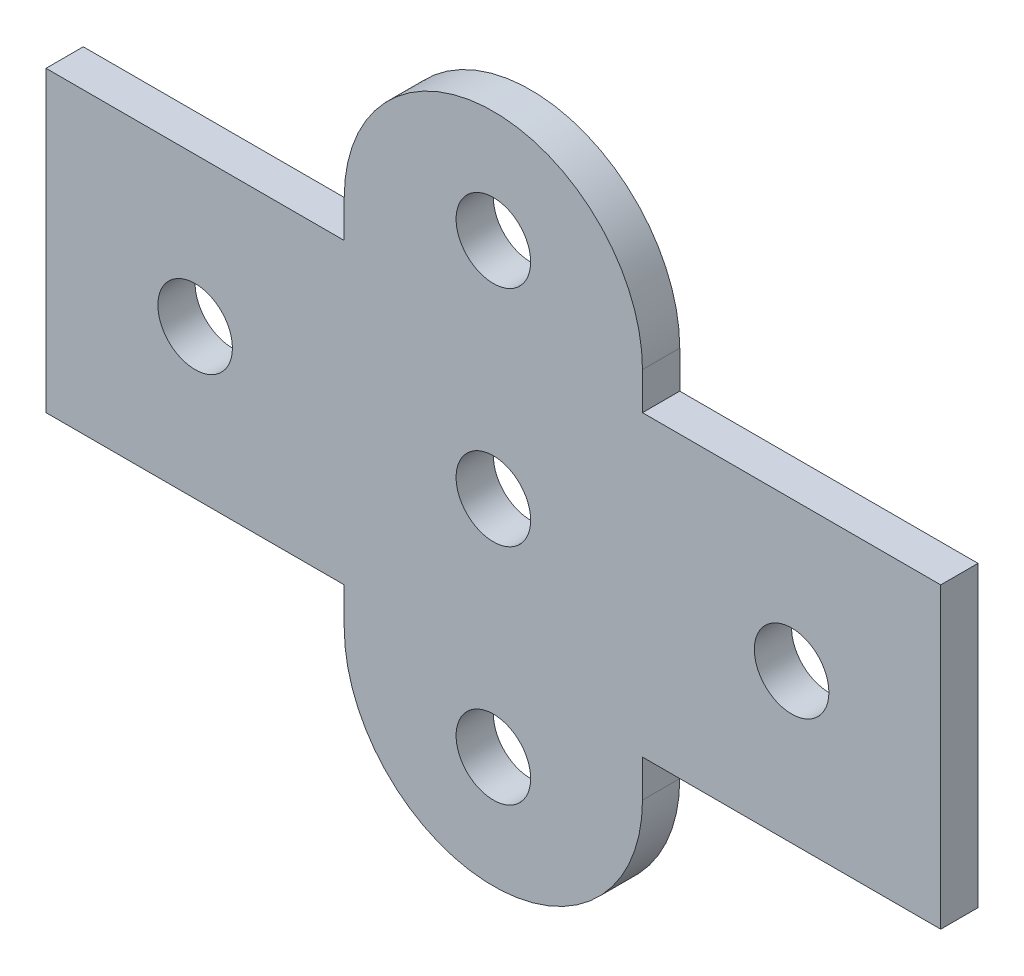
SolidWorks part; units mm, degrees
ref_plane "Front Plane" through (0, 0, 0) normal (0, 0, 1) x (1, 0, 0)
ref_plane "Top Plane" through (0, 0, 0) normal (0, 1, 0) x (1, 0, 0)
ref_plane "Right Plane" through (0, 0, 0) normal (1, 0, 0) x (0, 0, -1)
sketch "Sketch1" plane through (0, 0, 0) normal (0, 0, 1) x (1, 0, 0)
  line L0 (0, 12.7) -> (25.4, 12.7) construction
  line L1 (0, 0) -> (25.4, 0) construction
  line L2 (0, 0) -> (0, 50.8) construction
  line L3 (0, 50.8) -> (25.4, 50.8) construction
  line L4 (25.4, 0) -> (25.4, 50.8) construction
  line L5 (12.7, 50.8) -> (12.7, 0) construction
  line L6 (0, 25.4) -> (25.4, 25.4) construction
  line L7 (25.4, 38.1) -> (0, 38.1) construction
  line L8 (0, 38.1) -> (-25.4, 38.1)
  line L9 (-25.4, 38.1) -> (-25.4, 12.7)
  line L10 (-25.4, 12.7) -> (0, 12.7)
  line L11 (25.4, 38.1) -> (50.8, 38.1)
  line L12 (50.8, 38.1) -> (50.8, 12.7)
  line L13 (50.8, 12.7) -> (25.4, 12.7)
  line L14 (25.4, 38.1) -> (25.4, 41.275)
  line L15 (0, 38.1) -> (0, 41.275)
  line L16 (25.4, 12.7) -> (25.4, 9.525)
  line L17 (0, 12.7) -> (0, 9.525)
  circle A0 centre (12.7, 44.45) radius 3.175
  circle A1 centre (12.7, 6.35) radius 3.175
  circle A2 centre (12.7, 44.45) radius 6.35 construction
  arc A3 (0, 41.275) -> (25.4, 41.275) centre (12.7, 41.275) cw
  arc A4 (0, 9.525) -> (25.4, 9.525) centre (12.7, 9.525) ccw
  circle A5 centre (12.7, 25.4) radius 3.175
  circle A6 centre (38.1, 25.4) radius 3.175
  circle A7 centre (-12.7, 25.4) radius 3.175
  point P34 (0, 0)
  dimension "D4" = 6.35
  dimension "D5" = 19.05
  dimension "D6" = 3.175
  dimension "D7" = 12.7
  dimension "D8" = 12.7
  dimension "D10" = 6.35
  dimension "D11" = 25.4
  dimension "D12" = 25.4
  dimension "D14" = 12.7
  dimension "D1" = 50.8
  dimension "D2" = 25.4
  dimension "D3" = 12.7
  dimension "D9" = 3.175
  dimension "D13" = 12.7
extrude "Boss-Extrude1" add sketch "Sketch1" along normal blind 3.175
